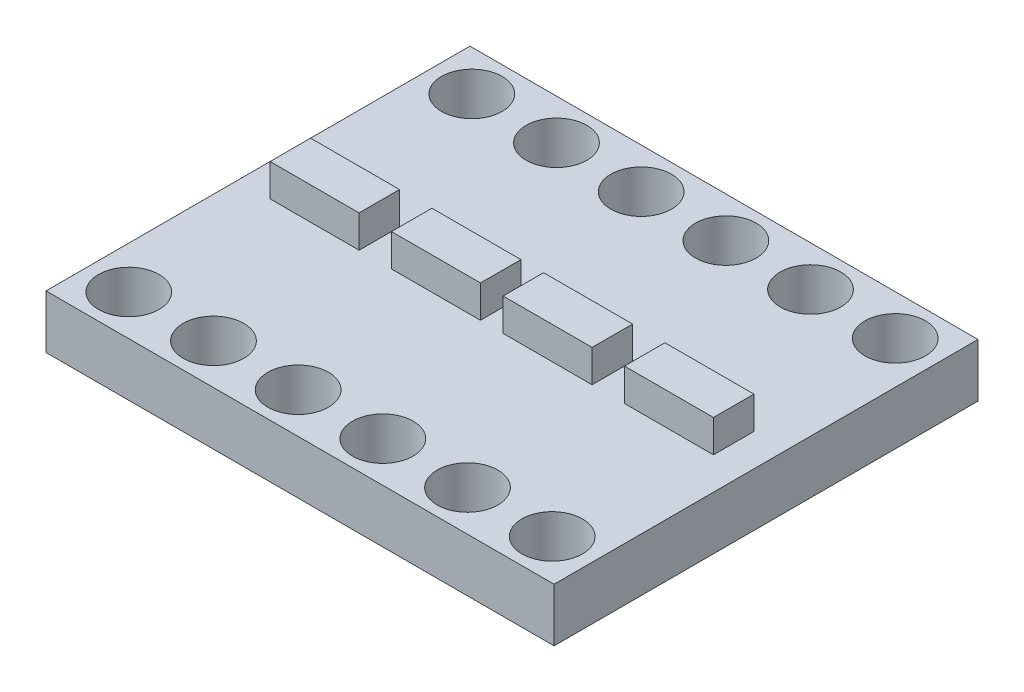
SolidWorks part; units mm, degrees
ref_plane "Front Plane" through (0, 0, 0) normal (0, 0, 1) x (1, 0, 0)
ref_plane "Top Plane" through (0, 0, 0) normal (0, 1, 0) x (1, 0, 0)
ref_plane "Right Plane" through (0, 0, 0) normal (1, 0, 0) x (0, 0, -1)
sketch "Sketch1" plane through (0, 0, 0) normal (0, 1, 0) x (1, 0, 0)
  line L1 (0, 0) -> (15.9512, 0)
  line L2 (0, 0) -> (0, 13.3096)
  line L3 (0, 13.3096) -> (15.9512, 13.3096)
  line L4 (15.9512, 0) -> (15.9512, 13.3096)
  dimension "D1" = 15.9512
  dimension "D2" = 13.3096
extrude "Boss-Extrude1" add sketch "Sketch1" along normal blind 1.6764
sketch "Sketch2" plane through (0, 1.6764, 0) normal (0, 1, 0) x (1, 0, 0)
  line L0 (0, 6.6548) -> (15.9512, 6.6548) construction
  line L1 (1.016, 7.2898) -> (3.81, 7.2898)
  line L2 (1.016, 7.2898) -> (1.016, 6.0198)
  line L3 (1.016, 6.0198) -> (3.81, 6.0198)
  line L4 (3.81, 7.2898) -> (3.81, 6.0198)
  line L5 (4.826, 7.2898) -> (7.62, 7.2898)
  line L6 (4.826, 7.2898) -> (4.826, 6.0198)
  line L7 (4.826, 6.0198) -> (7.62, 6.0198)
  line L8 (7.62, 7.2898) -> (7.62, 6.0198)
  line L9 (8.3312, 7.2898) -> (11.1252, 7.2898)
  line L10 (8.3312, 7.2898) -> (8.3312, 6.0198)
  line L11 (8.3312, 6.0198) -> (11.1252, 6.0198)
  line L12 (11.1252, 7.2898) -> (11.1252, 6.0198)
  line L13 (12.1412, 7.2898) -> (14.9352, 7.2898)
  line L14 (12.1412, 7.2898) -> (12.1412, 6.0198)
  line L15 (12.1412, 6.0198) -> (14.9352, 6.0198)
  line L16 (14.9352, 7.2898) -> (14.9352, 6.0198)
  line L17 (0, 13.3096) -> (0, 0) construction
  line L18 (15.9512, 0) -> (15.9512, 13.3096) construction
  point P22 (4.826, 6.6548)
  point P23 (8.3312, 6.6548)
  point P24 (12.1412, 6.6548)
  point P25 (4.6387, 6.6548)
  point P26 (1.016, 6.6548)
  dimension "D1" = 1.27
  dimension "D2" = 1.27
  dimension "D3" = 1.27
  dimension "D4" = 1.27
  dimension "D5" = 2.794
  dimension "D6" = 2.794
  dimension "D7" = 2.794
  dimension "D8" = 2.794
  dimension "D9" = 1.016
  dimension "D10" = 1.016
  dimension "D11" = 1.016
  dimension "D12" = 1.016
extrude "Boss-Extrude2" add sketch "Sketch2" along normal blind 1.016
sketch "Sketch3" plane through (0, 1.6764, 0) normal (0, 1, 0) x (1, 0, 0)
  line L0 (0, 13.3096) -> (0, 12.0396) construction
  line L1 (0, 13.3096) -> (0, 0) construction
  line L2 (0, 12.0396) -> (1.3293, 12.0396) construction
  line L3 (0, 6.6548) -> (15.9512, 6.6548) construction
  line L4 (15.9512, 0) -> (15.9512, 13.3096) construction
  line L5 (0, 1.27) -> (1.3293, 1.27) construction
  line L6 (0, 0) -> (0, 1.27) construction
  circle A0 centre (1.3293, 12.0396) radius 0.9525
  circle A6 centre (3.9878, 12.0396) radius 0.9525
  circle A7 centre (6.6464, 12.0396) radius 0.9525
  circle A8 centre (9.3049, 12.0396) radius 0.9525
  circle A9 centre (11.9634, 12.0396) radius 0.9525
  circle A10 centre (14.622, 12.0396) radius 0.9525
  circle A11 centre (14.622, 1.27) radius 0.9525
  circle A12 centre (11.9634, 1.27) radius 0.9525
  circle A13 centre (9.3049, 1.27) radius 0.9525
  circle A14 centre (6.6464, 1.27) radius 0.9525
  circle A15 centre (3.9878, 1.27) radius 0.9525
  circle A16 centre (1.3293, 1.27) radius 0.9525
  dimension "D1" = 1.905
  dimension "D2" = 1.27
  dimension "D3" = 1.3293
  dimension "D4" = 6
extrude "Cut-Extrude1" cut sketch "Sketch3" against normal through all
